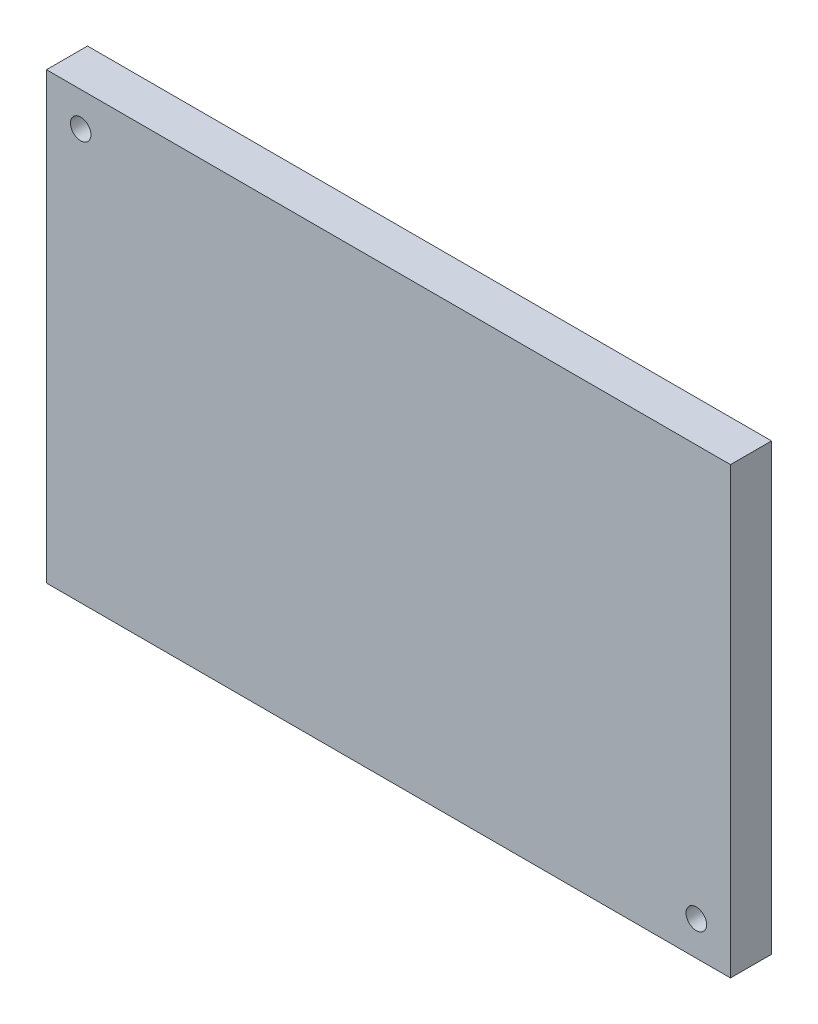
SolidWorks part; units mm, degrees
ref_plane "Plan de face" through (0, 0, 0) normal (0, 0, 1) x (1, 0, 0)
ref_plane "Plan de dessus" through (0, 0, 0) normal (0, 1, 0) x (1, 0, 0)
ref_plane "Plan de droite" through (0, 0, 0) normal (1, 0, 0) x (0, 0, -1)
sketch "Esquisse1" plane through (0, 0, 0) normal (0, 0, 1) x (1, 0, 0)
  line L1 (-50, 32.5) -> (50, 32.5)
  line L2 (-50, 32.5) -> (-50, -32.5)
  line L3 (-50, -32.5) -> (50, -32.5)
  line L4 (50, 32.5) -> (50, -32.5)
  dimension "D1" = 65
  dimension "D2" = 100
  dimension "D3" = 50
  dimension "D4" = 32.5
extrude "Boss.-Extru.1" add sketch "Esquisse1" along normal blind 6
sketch "Esquisse2" plane through (0, 0, 6) normal (0, 0, 1) x (1, 0, 0)
  line L0 (-50, -32.5) -> (50, -32.5) construction
  line L2 (50, -32.5) -> (50, 32.5) construction
  line L3 (50, 32.5) -> (-50, 32.5) construction
  line L4 (-50, 32.5) -> (-50, -32.5) construction
  circle A0 centre (-45, 27.5) radius 1.5
  circle A1 centre (45, -27.5) radius 1.5
  point P8 (50, -28.5465)
  dimension "D1" = 3
  dimension "D2" = 3
  dimension "D3" = 5
  dimension "D4" = 5
  dimension "D5" = 5
  dimension "D6" = 5
extrude "Enlèv. mat.-Extru.1" cut sketch "Esquisse2" against normal blind 6
equation "\"D3@Esquisse1\"=\"D2@Esquisse1\"/2"
equation "\"D4@Esquisse1\"=\"D1@Esquisse1\"/2"
